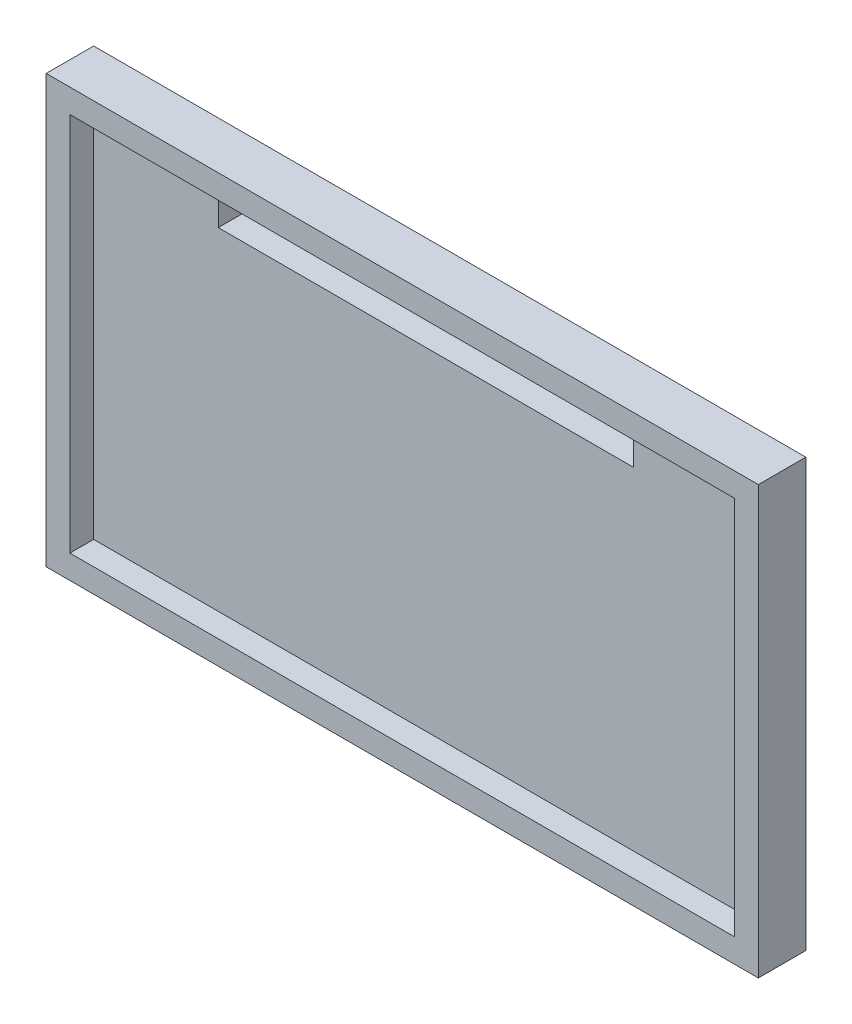
SolidWorks part; units mm, degrees
material "ﾊﾞﾙｻ"
ref_plane "正面" through (0, 0, 0) normal (0, 0, 1) x (1, 0, 0)
ref_plane "平面" through (0, 0, 0) normal (0, 1, 0) x (1, 0, 0)
ref_plane "右側面" through (0, 0, 0) normal (1, 0, 0) x (0, 0, -1)
sketch "ｽｹｯﾁ1" plane through (0, 0, 0) normal (0, 0, 1) x (1, 0, 0)
  line L0 (0, 14) -> (0, 0) construction
  line L1 (-30, 18) -> (30, 18)
  line L2 (-30, 18) -> (-30, -18)
  line L3 (-30, -18) -> (30, -18)
  line L4 (30, 18) -> (30, -18)
  line L5 (-30, 18) -> (30, -18) construction
  line L6 (-30, -18) -> (30, 18) construction
  line L7 (-17.5, 16) -> (17.5, 16)
  line L8 (-17.5, 16) -> (-17.5, 12)
  line L9 (-17.5, 12) -> (17.5, 12)
  line L10 (17.5, 16) -> (17.5, 12)
  line L11 (-17.5, 16) -> (17.5, 12) construction
  line L12 (-17.5, 12) -> (17.5, 16) construction
  point P0 (0, 0)
  point P6 (0, 14)
  dimension "D1" = 4
  dimension "D2" = 35
  dimension "D3" = 36
  dimension "D4" = 2
  dimension "D5" = 60
extrude "ﾎﾞｽ - 押し出し1" add sketch "ｽｹｯﾁ1" along normal blind 2
sketch "ｽｹｯﾁ2" plane through (0, 0, 2) normal (0, 0, 1) x (1, 0, 0)
  line L0 (30, 18) -> (-30, 18) construction
  line L1 (30, 18) -> (-30, 18)
  line L2 (-30, 18) -> (-30, -18) construction
  line L3 (-30, 18) -> (-30, -18)
  line L4 (30, -18) -> (30, 18) construction
  line L5 (-30, -18) -> (30, -18) construction
  line L6 (30, -18) -> (30, 18)
  line L7 (-30, -18) -> (30, -18)
  line L8 (28, 16) -> (-28, 16)
  line L9 (-28, 16) -> (-28, -16)
  line L10 (-28, -16) -> (28, -16)
  line L11 (28, -16) -> (28, 16)
  dimension "D1" = 2
extrude "ﾎﾞｽ - 押し出し2" add sketch "ｽｹｯﾁ2" along normal blind 2
